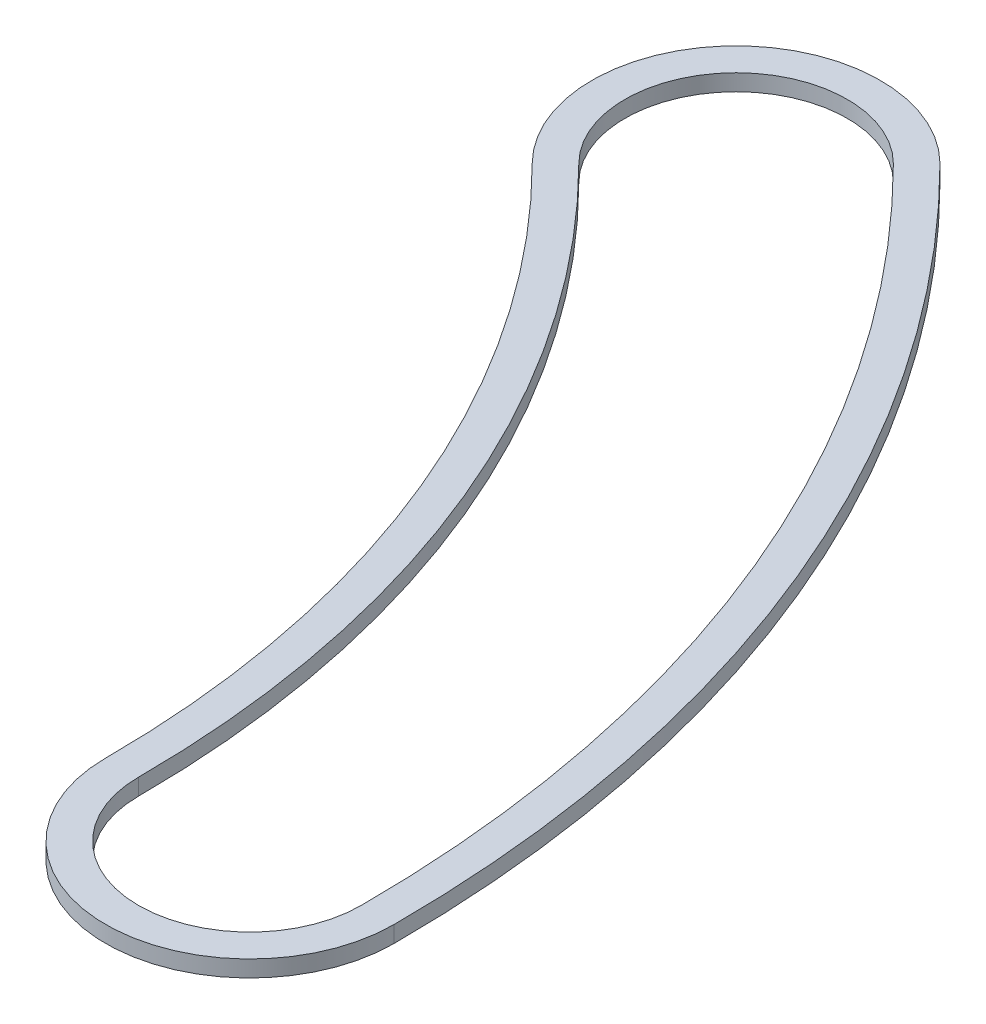
SolidWorks part; units mm, degrees
material "NBR"
ref_plane "Front Plane" through (0, 0, 0) normal (0, 0, 1) x (1, 0, 0)
ref_plane "Top Plane" through (0, 0, 0) normal (0, 1, 0) x (1, 0, 0)
ref_plane "Right Plane" through (0, 0, 0) normal (1, 0, 0) x (0, 0, -1)
sketch "Sketch1" plane through (0, 0, 0) normal (0, 1, 0) x (1, 0, 0)
  line L0 (0, 0) -> (25.5937, 25.5937) construction
  line L1 (0, 0) -> (36.195, 0) construction
  arc A0 (36.195, 0) -> (25.5937, 25.5937) centre (0, 0) ccw construction
  arc A1 (40.64, 0) -> (28.7368, 28.7368) centre (0, 0) ccw
  arc A2 (31.75, 0) -> (22.4506, 22.4506) centre (0, 0) ccw
  arc A3 (31.75, 0) -> (40.64, 0) centre (36.195, 0) ccw
  arc A4 (28.7368, 28.7368) -> (22.4506, 22.4506) centre (25.5937, 25.5937) ccw
  arc A5 (36.195, 0) -> (25.5937, 25.5937) centre (0, 0) ccw construction
  arc A6 (39.624, 0) -> (28.0184, 28.0184) centre (0, 0) ccw
  arc A7 (32.766, 0) -> (23.1691, 23.1691) centre (0, 0) ccw
  arc A8 (32.766, 0) -> (39.624, 0) centre (36.195, 0) ccw
  arc A9 (28.0184, 28.0184) -> (23.1691, 23.1691) centre (25.5937, 25.5937) ccw
  point P4 (33.4398, 13.8512)
  point P13 (33.4398, 13.8512)
  dimension "D4" = 36.195
  dimension "D3" = 4.445
  dimension "D1" = 45
  dimension "D2" = 1.016
extrude "Boss-Extrude1" add sketch "Sketch1" along normal blind 0.508
equation "\"w\"= 0.04"
equation "\"D2@Sketch1\"=\"w\""
equation "\"D3@Sketch1\"= .185 - .01 '10 thou smaller than channel rad"
